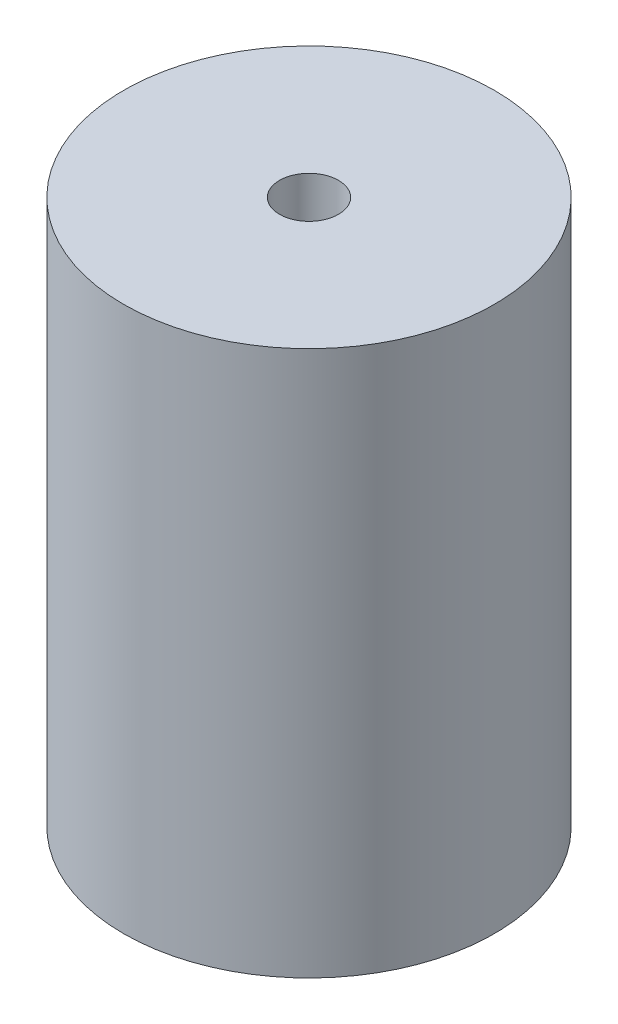
SolidWorks part; units mm, degrees
ref_plane "Front Plane" through (0, 0, 0) normal (0, 0, 1) x (1, 0, 0)
ref_plane "Top Plane" through (0, 0, 0) normal (0, 1, 0) x (1, 0, 0)
ref_plane "Right Plane" through (0, 0, 0) normal (1, 0, 0) x (0, 0, -1)
sketch "Sketch1" plane through (0, 0, 0) normal (0, 1, 0) x (1, 0, 0)
  circle A0 centre (0, 0) radius 12.7
  dimension "D1" = 25.4
extrude "Boss-Extrude1" add sketch "Sketch1" along normal mid plane 37.338
hole_wizard "Tap Drill for #10-32 Tap1" positions "Sketch2" profile "Sketch3" hole size "#10-32" standard "ANSI Inch" end condition up to next
sketch "Sketch2" plane through (0, 18.669, 0) normal (0, 1, 0) x (1, 0, 0)
  point P0 (0, 0)
sketch "Sketch3" plane through (0, 18.669, 0) normal (1, 0, 0) x (0, 0, 1)
  line L0 (0, 0) -> (0, 37.338)
  line L1 (0, 37.338) -> (2.0193, 37.338)
  line L2 (2.0193, 37.338) -> (2.0193, 0)
  line L5 (2.0193, 0) -> (0, 0)
  line L11 (0, -6.35) -> (0, 107.95) construction
  dimension "Thru Hole Dia." = 4.0386
  dimension "Thru Hole Depth" = 37.338
